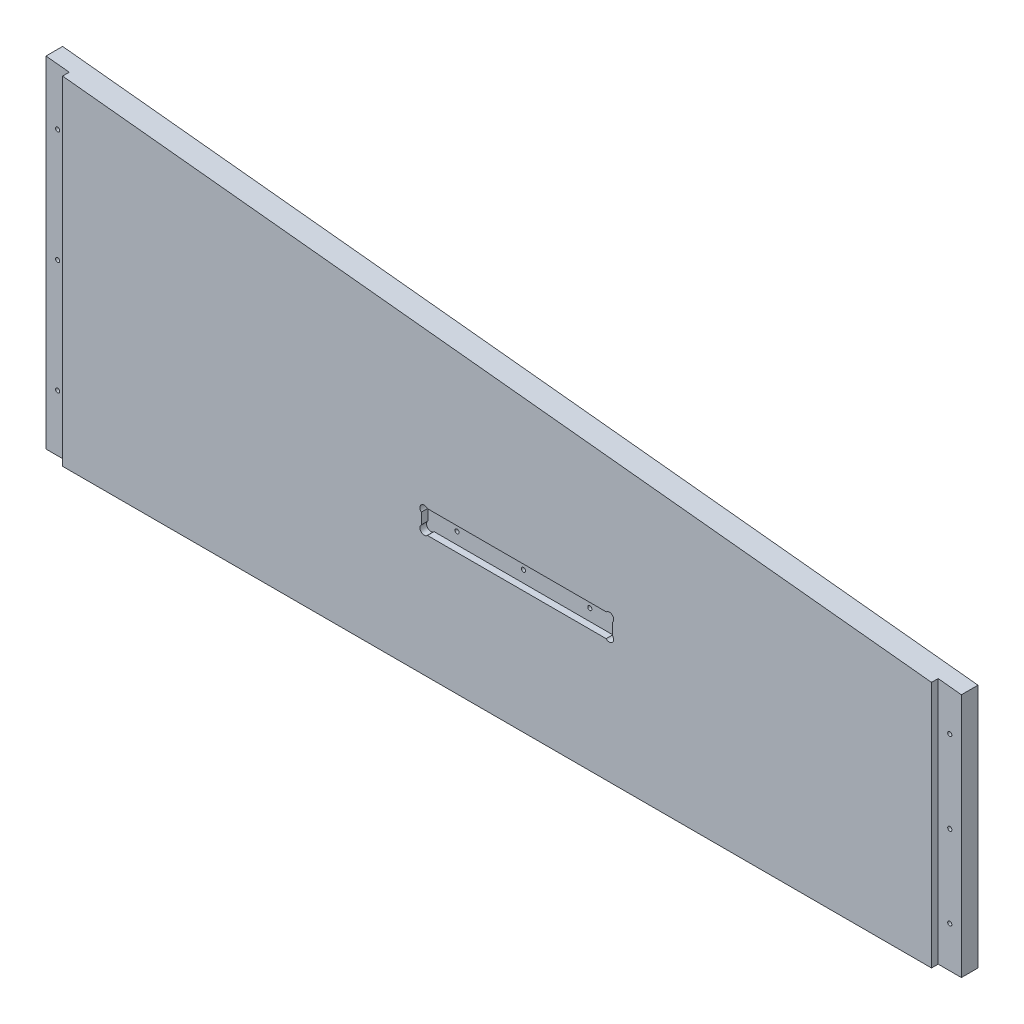
SolidWorks part; units mm, degrees
material "Maple"
ref_plane "Front Plane" through (0, 0, 0) normal (0, 0, 1) x (1, 0, 0)
ref_plane "Top Plane" through (0, 0, 0) normal (0, 1, 0) x (1, 0, 0)
ref_plane "Right Plane" through (0, 0, 0) normal (1, 0, 0) x (0, 0, -1)
sketch "Sketch1" plane through (0, 0, 0) normal (0, 0, 1) x (1, 0, 0)
  line L0 (-163.9887, -5335.905) -> (-163.9887, -5432.425)
  line L1 (-102.87, -5350.891) -> (-33.02, -5350.891)
  line L2 (-111.8235, -5341.9375) -> (-111.8235, -5334)
  line L3 (-24.0665, -5341.9375) -> (-24.0665, -5334)
  line L4 (-298.9262, -5332.73) -> (-167.1637, -5332.73)
  line L5 (-167.1637, -5435.6) -> (-298.9262, -5435.6)
  line L6 (-302.1012, -5432.425) -> (-302.1012, -5335.905)
  line L7 (-107.6325, -5329.809) -> (-28.2575, -5329.809)
  line L8 (174.9425, -5308.6) -> (174.9425, -5581.65)
  line L9 (449.2625, -5413.1661) -> (449.2625, -5421.9659)
  line L10 (595.3125, -5421.9659) -> (595.3125, -5413.1661)
  line L11 (839.47, -5509.5521) -> (839.47, -5307.6729)
  line L12 (839.47, -5307.6729) -> (863.6, -5307.6729)
  line L13 (839.47, -5509.5521) -> (863.6, -5509.5521)
  line L14 (863.6, -5509.5521) -> (863.6, -5307.6729)
  line L15 (-354.2665, -5341.9375) -> (-354.2665, -5334)
  line L16 (-100.8856, -5889.625) -> (-50.0856, -5889.625)
  line L17 (-104.0606, -5969) -> (-104.0606, -5892.8)
  line L18 (-46.9106, -5892.8) -> (-46.9106, -5969)
  line L19 (-50.0856, -5972.175) -> (-100.8856, -5972.175)
  line L20 (-100.8856, -5848.35) -> (-50.0856, -5848.35)
  line L21 (857.25, -5502.275) -> (157.1625, -5575.3)
  line L22 (857.25, -5314.95) -> (857.25, -5502.275)
  line L23 (157.1625, -5314.95) -> (157.1625, -5575.3)
  line L24 (857.25, -5314.95) -> (157.1625, -5314.95)
  line L25 (150.8125, -5308.6) -> (174.9425, -5308.6)
  line L26 (174.9425, -5581.65) -> (150.8125, -5581.65)
  line L27 (137.16, -5314.95) -> (137.16, -5502.275)
  line L28 (150.8125, -5581.65) -> (150.8125, -5308.6)
  line L29 (590.8224, -5408.676) -> (453.7526, -5408.676)
  line L30 (453.7526, -5426.456) -> (590.8224, -5426.456)
  line L31 (137.16, -6013.45) -> (137.16, -5867.4)
  line L32 (150.8125, -5746.75) -> (150.8125, -6019.8)
  line L33 (143.51, -5639.9938) -> (143.51, -5654.294)
  line L34 (590.8224, -5919.724) -> (453.7526, -5919.724)
  line L35 (453.7526, -5901.944) -> (590.8224, -5901.944)
  line L36 (449.2625, -5915.2339) -> (449.2625, -5906.4341)
  line L37 (174.9425, -6019.8) -> (174.9425, -5746.75)
  line L38 (595.3125, -5906.4341) -> (595.3125, -5915.2339)
  line L39 (839.47, -5818.8479) -> (839.47, -6020.7271)
  line L40 (839.47, -5818.8479) -> (863.6, -5818.8479)
  line L41 (863.6, -5818.8479) -> (863.6, -6020.7271)
  line L42 (839.47, -6020.7271) -> (863.6, -6020.7271)
  line L43 (-155.8782, -5867.4) -> (-603.25, -5867.4)
  line L44 (-433.07, -5350.891) -> (-363.22, -5350.891)
  line L45 (-437.8325, -5329.809) -> (-358.4575, -5329.809)
  line L46 (889, -6045.2) -> (-635, -6045.2)
  line L47 (-635, -5283.2) -> (889, -5283.2)
  line L48 (-635, -6045.2) -> (-635, -5283.2)
  line L49 (889, -5283.2) -> (889, -6045.2)
  line L50 (137.16, -5502.275) -> (-603.25, -5502.275)
  line L51 (-603.25, -5314.95) -> (137.16, -5314.95)
  line L52 (143.51, -5654.294) -> (-609.6, -5654.294)
  line L53 (-609.6, -5639.9938) -> (143.51, -5639.9938)
  line L54 (137.16, -5536.0062) -> (-603.25, -5536.0062)
  line L55 (-603.25, -5794.375) -> (137.16, -5794.375)
  line L56 (-603.25, -6013.45) -> (137.16, -6013.45)
  line L57 (-603.25, -5536.0062) -> (-603.25, -5794.375)
  line L58 (137.16, -5794.375) -> (137.16, -5536.0062)
  line L59 (-609.6, -5654.294) -> (-609.6, -5639.9938)
  line L60 (-603.25, -5867.4) -> (-603.25, -6013.45)
  line L61 (-603.25, -5314.95) -> (-603.25, -5502.275)
  line L62 (-442.0235, -5341.9375) -> (-442.0235, -5334)
  line L63 (857.25, -5826.125) -> (157.1625, -5753.1)
  line L64 (857.25, -6013.45) -> (857.25, -5826.125)
  line L65 (157.1625, -6013.45) -> (157.1625, -5753.1)
  line L66 (857.25, -6013.45) -> (157.1625, -6013.45)
  line L67 (174.9425, -5746.75) -> (150.8125, -5746.75)
  line L68 (150.8125, -6019.8) -> (174.9425, -6019.8)
  line L69 (137.16, -5867.4) -> (4.907, -5867.4)
  circle A0 centre (-36.195, -5484.0124) radius 1.5875
  arc A1 (-298.9262, -5332.73) -> (-302.1012, -5335.905) centre (-298.9262, -5335.905) ccw
  arc A2 (-302.1012, -5432.425) -> (-298.9262, -5435.6) centre (-298.9262, -5432.425) ccw
  arc A3 (-163.9887, -5335.905) -> (-167.1637, -5332.73) centre (-167.1637, -5335.905) ccw
  arc A4 (-167.1637, -5435.6) -> (-163.9887, -5432.425) centre (-167.1637, -5432.425) ccw
  arc A5 (-111.8235, -5341.9375) -> (-102.87, -5350.891) centre (-102.87, -5341.9375) ccw
  arc A6 (-107.6325, -5329.809) -> (-111.8235, -5334) centre (-107.6325, -5334) ccw
  circle A7 centre (166.0525, -5444.6613) radius 1.5875
  circle A8 centre (166.0525, -5358.1871) radius 1.5875
  circle A9 centre (471.4875, -5417.566) radius 1.5875
  arc A10 (453.7526, -5408.676) -> (449.2625, -5413.1661) centre (451.5076, -5410.9211) ccw
  arc A11 (449.2625, -5421.9659) -> (453.7526, -5426.456) centre (451.5076, -5424.2109) ccw
  circle A12 centre (522.2875, -5417.566) radius 1.5875
  circle A13 centre (573.0875, -5417.566) radius 1.5875
  arc A14 (590.8224, -5426.456) -> (595.3125, -5421.9659) centre (593.0674, -5424.2109) ccw
  arc A15 (595.3125, -5413.1661) -> (590.8224, -5408.676) centre (593.0674, -5410.9211) ccw
  circle A16 centre (848.36, -5471.8269) radius 1.5875
  circle A17 centre (848.36, -5409.0762) radius 1.5875
  circle A18 centre (848.36, -5346.3254) radius 1.5875
  arc A19 (-363.22, -5350.891) -> (-354.2665, -5341.9375) centre (-363.22, -5341.9375) ccw
  arc A20 (-354.2665, -5334) -> (-358.4575, -5329.809) centre (-358.4575, -5334) ccw
  arc A21 (-24.0665, -5334) -> (-28.2575, -5329.809) centre (-28.2575, -5334) ccw
  arc A22 (-33.02, -5350.891) -> (-24.0665, -5341.9375) centre (-33.02, -5341.9375) ccw
  circle A23 centre (-86.995, -5484.0124) radius 1.5875
  circle A24 centre (-333.4544, -5894.07) radius 2.54
  circle A25 centre (-333.4544, -5994.4) radius 2.54
  arc A26 (-104.0606, -5969) -> (-100.8856, -5972.175) centre (-100.8856, -5969) ccw
  arc A27 (-50.0856, -5972.175) -> (-46.9106, -5969) centre (-50.0856, -5969) ccw
  arc A28 (-100.8856, -5848.35) -> (-128.3819, -5857.875) centre (-100.8856, -5892.8) ccw
  arc A29 (-155.8782, -5867.4) -> (-128.3819, -5857.875) centre (-155.8782, -5822.95) ccw
  arc A30 (-22.5893, -5857.875) -> (-50.0856, -5848.35) centre (-50.0856, -5892.8) ccw
  circle A31 centre (-132.6356, -5894.07) radius 2.54
  circle A32 centre (-132.6356, -5994.4) radius 2.54
  arc A33 (-46.9106, -5892.8) -> (-50.0856, -5889.625) centre (-50.0856, -5892.8) ccw
  arc A34 (-100.8856, -5889.625) -> (-104.0606, -5892.8) centre (-100.8856, -5892.8) ccw
  arc A35 (-22.5893, -5857.875) -> (4.907, -5867.4) centre (4.907, -5822.95) ccw
  circle A36 centre (166.0525, -5531.1356) radius 1.5875
  arc A37 (449.2625, -5915.2339) -> (453.7526, -5919.724) centre (451.5076, -5917.4789) ccw
  arc A38 (453.7526, -5901.944) -> (449.2625, -5906.4341) centre (451.5076, -5904.1891) ccw
  circle A39 centre (166.0525, -5797.2644) radius 1.5875
  circle A40 centre (166.0525, -5883.7387) radius 1.5875
  circle A41 centre (166.0525, -5970.2129) radius 1.5875
  circle A42 centre (471.4875, -5910.834) radius 1.5875
  circle A43 centre (522.2875, -5910.834) radius 1.5875
  circle A44 centre (573.0875, -5910.834) radius 1.5875
  arc A45 (595.3125, -5906.4341) -> (590.8224, -5901.944) centre (593.0674, -5904.1891) ccw
  arc A46 (590.8224, -5919.724) -> (595.3125, -5915.2339) centre (593.0674, -5917.4789) ccw
  circle A47 centre (848.36, -5919.3238) radius 1.5875
  circle A48 centre (848.36, -5982.0746) radius 1.5875
  circle A49 centre (848.36, -5856.5731) radius 1.5875
  arc A50 (-437.8325, -5329.809) -> (-442.0235, -5334) centre (-437.8325, -5334) ccw
  circle A51 centre (-429.895, -5484.0124) radius 1.5875
  arc A52 (-442.0235, -5341.9375) -> (-433.07, -5350.891) centre (-433.07, -5341.9375) ccw
  circle A53 centre (-379.095, -5484.0124) radius 1.5875
sketch "HeadSideRightOutline" plane through (0, 0, 0) normal (0, 0, 1) x (1, 0, 0)
  line L0 (174.9425, -6013.45) -> (839.47, -6013.45)
  line L1 (839.47, -6013.45) -> (839.47, -5824.2704)
  line L2 (839.47, -5824.2704) -> (174.9425, -5754.9546)
  line L3 (174.9425, -5754.9546) -> (174.9425, -6013.45)
extrude "HeadSideRight_Thickness" add sketch "HeadSideRightOutline" against normal blind 17.78
sketch "Sketch10" plane through (0, 0, -17.78) normal (0, 0, -1) x (-1, 0, 0)
  line L0 (-174.9425, -6013.45) -> (-157.1625, -6013.45)
  line L1 (-157.1625, -6013.45) -> (-157.1625, -5753.1)
  line L2 (-157.1625, -5753.1) -> (-174.9425, -5754.9546)
  line L3 (-174.9425, -5754.9546) -> (-174.9425, -6013.45)
  line L4 (-839.47, -6013.45) -> (-857.25, -6013.45)
  line L5 (-857.25, -6013.45) -> (-857.25, -5826.125)
  line L6 (-857.25, -5826.125) -> (-839.47, -5824.2704)
  line L7 (-839.47, -5824.2704) -> (-839.47, -6013.45)
  line L8 (-857.25, -5826.125) -> (-157.1625, -5753.1) construction
  dimension "D1" = 17.78
  dimension "D2" = 17.78
extrude "Extrude4" add sketch "Sketch10" against normal blind 12.7
sketch "Sketch8" plane through (0, 0, 0) normal (0, 0, 1) x (1, 0, 0)
  circle A0 centre (166.0525, -5970.2129) radius 1.5875
  circle A1 centre (166.0525, -5883.7387) radius 1.5875
  circle A2 centre (166.0525, -5797.2644) radius 1.5875
  circle A3 centre (848.36, -5982.0746) radius 1.5875
  circle A4 centre (848.36, -5919.3238) radius 1.5875
  circle A5 centre (848.36, -5856.5731) radius 1.5875
  circle A6 centre (471.4875, -5910.834) radius 1.5875
  circle A7 centre (522.2875, -5910.834) radius 1.5875
  circle A8 centre (573.0875, -5910.834) radius 1.5875
extrude "Cut-Extrude4" cut sketch "Sketch8" against normal up to surface (17.78 mm away) up to face at (507.2062, -5901.5312, -17.78)
sketch "Sketch9" plane through (0, 0, 0) normal (0, 0, 1) x (1, 0, 0)
  line L12 (449.2625, -5919.724) -> (595.3125, -5919.724)
  line L13 (449.2625, -5901.944) -> (595.3125, -5901.944)
  line L14 (449.2625, -5901.944) -> (449.2625, -5919.724)
  line L15 (595.3125, -5901.944) -> (595.3125, -5919.724)
  dimension "D1" = 17.78
extrude "Cut-Extrude5" cut sketch "Sketch9" against normal blind 5.08
sketch "Sketch11" plane through (0, 0, 0) normal (0, 0, 1) x (1, 0, 0)
  line L0 (595.3125, -5901.944) -> (593.0674, -5904.1891) construction
  line L1 (595.3125, -5919.724) -> (593.0674, -5917.4789) construction
  line L2 (449.2625, -5919.724) -> (451.5076, -5917.4789) construction
  line L3 (449.2625, -5901.944) -> (451.5076, -5904.1891) construction
  line L4 (449.2625, -5919.724) -> (595.3125, -5919.724) construction
  line L5 (595.3125, -5901.944) -> (449.2625, -5901.944) construction
  line L6 (449.2625, -5919.724) -> (595.3125, -5919.724) construction
  line L7 (595.3125, -5901.944) -> (449.2625, -5901.944) construction
  circle A0 centre (451.5076, -5904.1891) radius 3.302
  circle A1 centre (451.5076, -5917.4789) radius 3.302
  circle A2 centre (593.0674, -5917.4789) radius 3.302
  circle A3 centre (593.0674, -5904.1891) radius 3.302
  dimension "D1" = 45
  dimension "D2" = 45
  dimension "D3" = 3.175
  dimension "D4" = 3.175
  dimension "D5" = 45
  dimension "D6" = 45
  dimension "D7" = 3.175
  dimension "D8" = 3.175
extrude "Cut-Extrude6" cut sketch "Sketch11" against normal up to surface (5.08 mm away) up to face at (523.875, -5910.834, -5.08)
